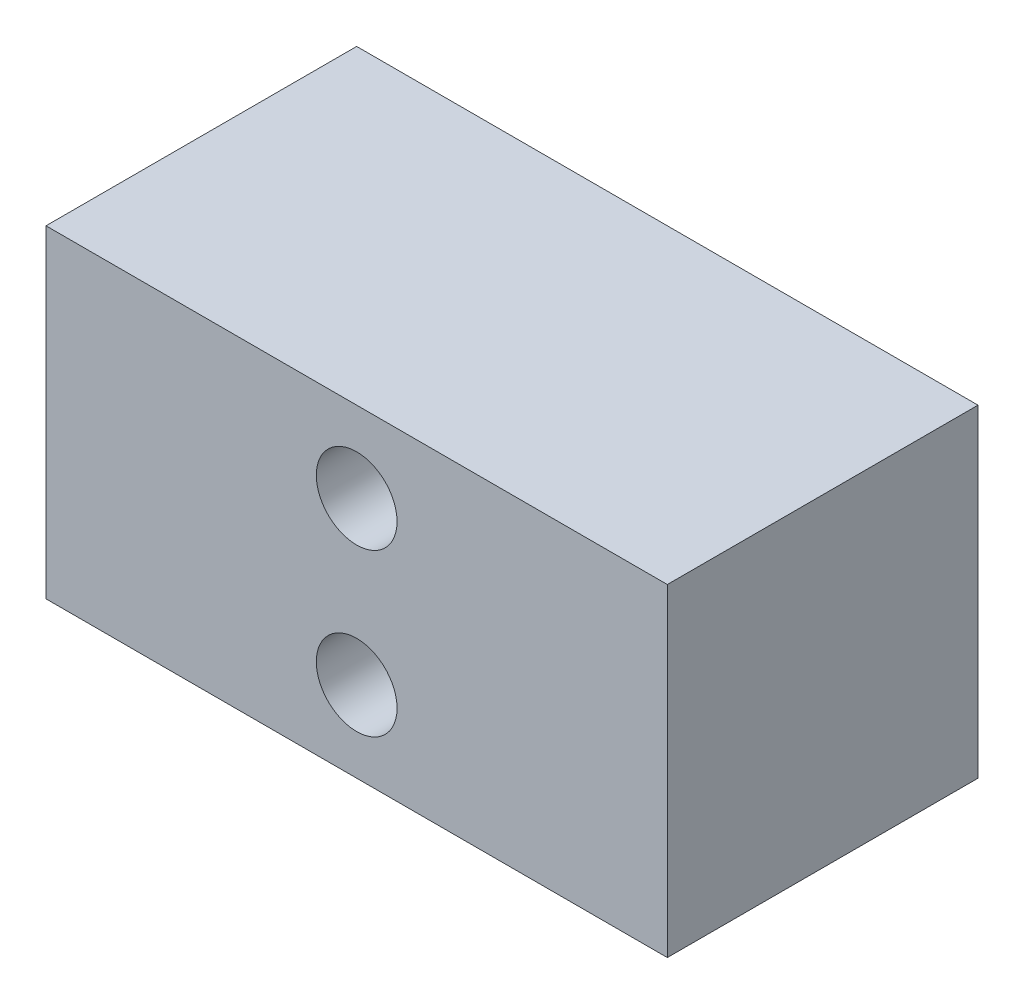
SolidWorks part; units mm, degrees
ref_plane "Front Plane" through (0, 0, 0) normal (0, 0, 1) x (1, 0, 0)
ref_plane "Top Plane" through (0, 0, 0) normal (0, 1, 0) x (1, 0, 0)
ref_plane "Right Plane" through (0, 0, 0) normal (1, 0, 0) x (0, 0, -1)
sketch "Sketch1" plane through (0, 0, 0) normal (0, 0, 1) x (1, 0, 0)
  line L1 (0, 0) -> (50.8, 0)
  line L2 (0, 0) -> (0, 26.416)
  line L3 (0, 26.416) -> (50.8, 26.416)
  line L4 (50.8, 0) -> (50.8, 26.416)
  circle A0 centre (25.4, 19.812) radius 3.302
  circle A1 centre (25.4, 6.604) radius 3.302
  dimension "D3" = 6.604
  dimension "D4" = 6.604
  dimension "D1" = 26.416
  dimension "D2" = 50.8
  dimension "D5" = 25.4
  dimension "D6" = 25.4
  dimension "D7" = 6.604
  dimension "D8" = 6.604
extrude "Boss-Extrude1" add sketch "Sketch1" along normal blind 25.4
